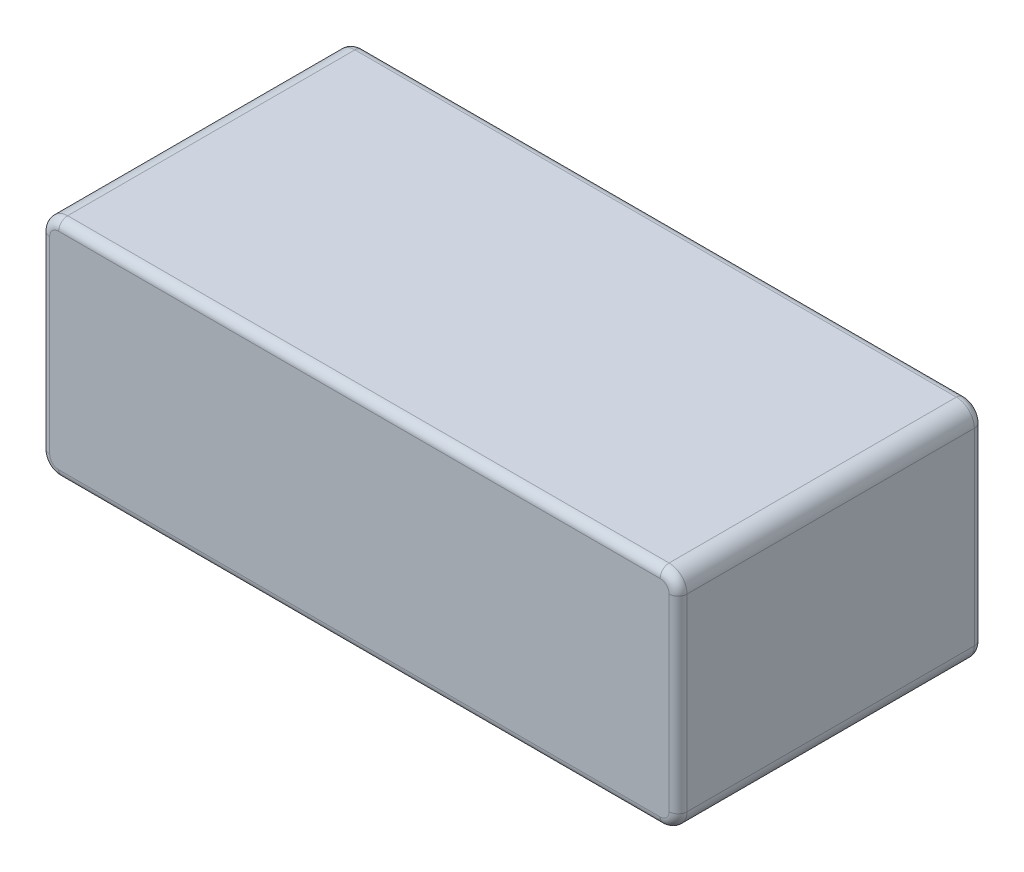
SolidWorks part; units mm, degrees
ref_plane "Ebene vorne" through (0, 0, 0) normal (0, 0, 1) x (1, 0, 0)
ref_plane "Ebene oben" through (0, 0, 0) normal (0, 1, 0) x (1, 0, 0)
ref_plane "Ebene rechts" through (0, 0, 0) normal (1, 0, 0) x (0, 0, -1)
sketch "Skizze1" plane through (0, 0, 0) normal (0, 0, 1) x (1, 0, 0)
  line L0 (0, 25) -> (0, 0)
  line L1 (0, 25) -> (71, 25)
  line L3 (0, 0) -> (71, 0)
  line L7 (71, 0) -> (71, 25)
  dimension "D1" = 25
  dimension "D6" = 71
extrude "Aufsatz-Linear austragen1" add sketch "Skizze1" along normal blind 34
fillet "Verrundung2" radius 2 1 edges at (71, 25, 17)
fillet "Verrundung3" radius 2 1 edges at (71, 0, 17)
fillet "Verrundung4" radius 2 1 edges at (0, 25, 17)
fillet "Verrundung5" radius 2 1 edges at (0, 0, 17)
fillet "Verrundung6" radius 1 8 edges at (70.4142, 24.4142, 34) (71, 12.5, 34) (70.4142, 0.5858, 34) (35.5, 0, 34) (0.5858, 0.5858, 34) (0, 12.5, 34) (0.5858, 24.4142, 34) (35.5, 25, 34)
fillet "Verrundung7" radius 1 8 edges at (70.4142, 24.4142, 0) (71, 12.5, 0) (70.4142, 0.5858, 0) (35.5, 0, 0) (0.5858, 0.5858, 0) (0, 12.5, 0) (0.5858, 24.4142, 0) (35.5, 25, 0)
sketch "Skizze3" plane through (0, 0, 0) normal (0, 0, -1) x (-1, 0, 0)
  line L1 (-4.25, 6) -> (4.25, 6)
  line L2 (-4.25, 6) -> (-4.25, 19)
  line L3 (-4.25, 19) -> (4.25, 19)
  line L4 (4.25, 6) -> (4.25, 19)
  line L5 (-4.25, 6) -> (4.25, 19) construction
  line L6 (-4.25, 19) -> (4.25, 6) construction
  line L7 (0, 23) -> (0, 2) construction
  point P0 (0, 12.5)
  dimension "D1" = 13
  dimension "D2" = 8.5
extrude "Aufsatz-Linear austragen2" [suppressed] add sketch "Skizze3" along normal blind 5
